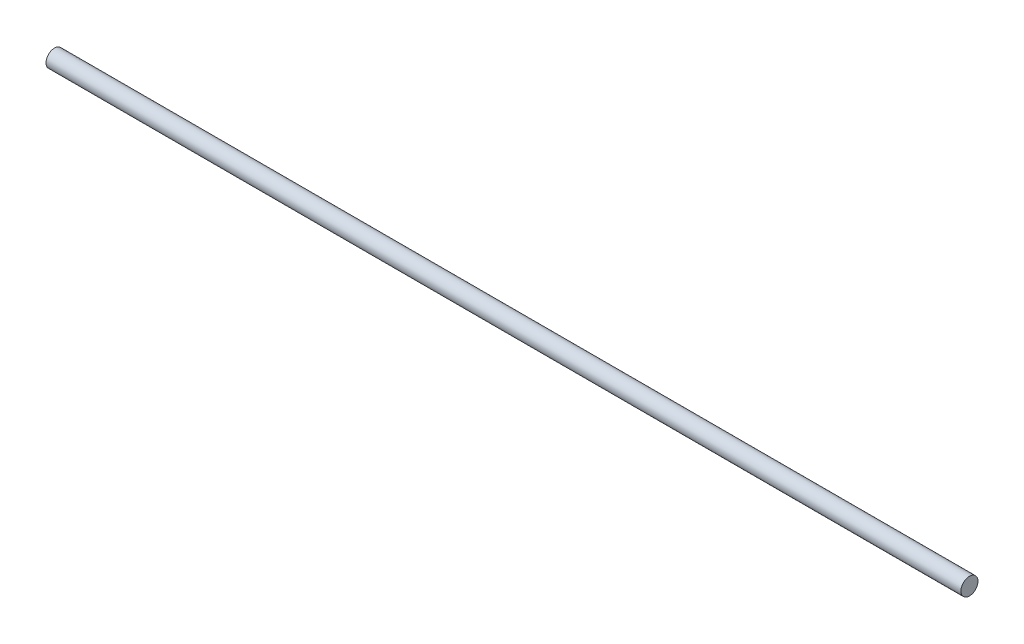
SolidWorks part; units mm, degrees
ref_plane "Front Plane" through (0, 0, 0) normal (0, 0, 1) x (1, 0, 0)
ref_plane "Top Plane" through (0, 0, 0) normal (0, 1, 0) x (1, 0, 0)
ref_plane "Right Plane" through (0, 0, 0) normal (1, 0, 0) x (0, 0, -1)
sketch "Sketch1" plane through (0, 0, 0) normal (1, 0, 0) x (0, 0, -1)
  circle A0 centre (0, 0) radius 4.2
  dimension "D1" = 8.4
extrude "Boss-Extrude1" add sketch "Sketch1" along normal blind 450
